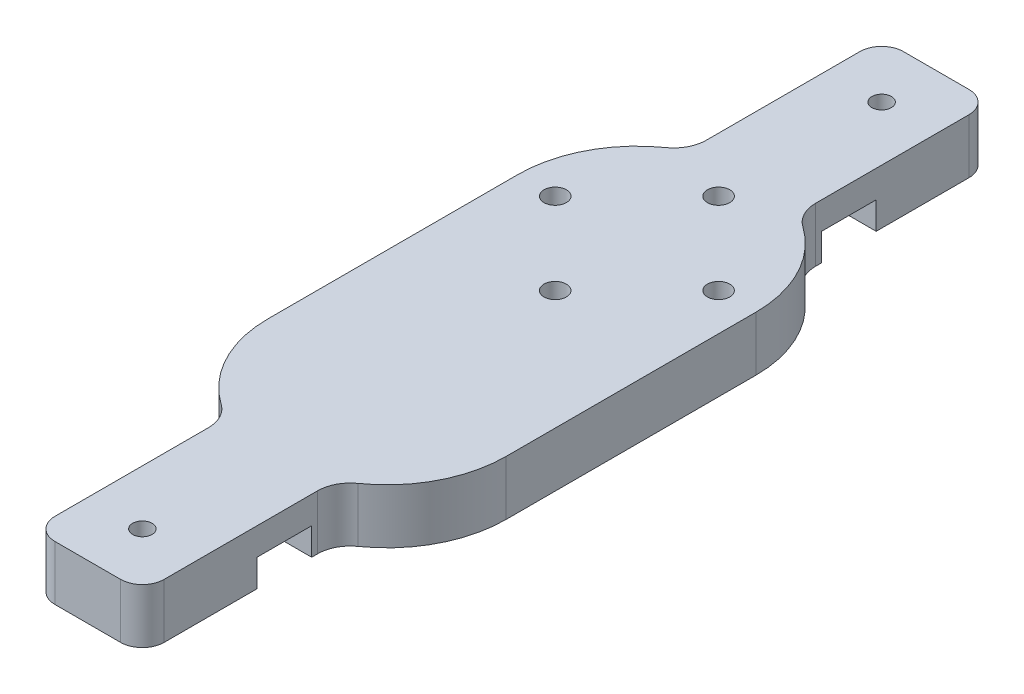
SolidWorks part; units mm, degrees
ref_plane "Front Plane" through (0, 0, 0) normal (0, 0, 1) x (1, 0, 0)
ref_plane "Top Plane" through (0, 0, 0) normal (0, 1, 0) x (1, 0, 0)
ref_plane "Right Plane" through (0, 0, 0) normal (1, 0, 0) x (0, 0, -1)
sketch "Sketch1" plane through (0, 0, 0) normal (0, 1, 0) x (1, 0, 0)
  line L0 (13.85, -23.7542) -> (13.85, 5.2917)
  line L1 (-13.85, 5.2917) -> (-13.85, -23.7542)
  line L2 (-13.85, 0) -> (13.85, 0) construction
  line L3 (0, 5.2917) -> (0, 14.7917) construction
  line L4 (0, 5.2917) -> (9.5, 5.2917) construction
  line L5 (0, 5.2917) -> (0, 14.7917) construction
  line L6 (0, 5.2917) -> (-9.5, 5.2917) construction
  line L7 (0, 5.2917) -> (0, -4.2083) construction
  line L8 (0, 0) -> (0, 40.1011) construction
  line L9 (0, 0) -> (0, -58.5637) construction
  line L10 (6.35, -36.0628) -> (6.35, -56.0237)
  line L12 (-6.35, -36.0628) -> (-6.35, -56.0237)
  line L14 (3.81, -58.5637) -> (-3.81, -58.5637)
  line L15 (3.81, 40.1011) -> (-3.81, 40.1011)
  line L16 (6.35, 17.6003) -> (6.35, 37.5611)
  line L17 (-6.35, 17.6003) -> (-6.35, 37.5611)
  line L18 (6.35, 0) -> (6.35, 40.1011) construction
  line L19 (0, 40.1011) -> (39.9619, 40.1011) construction
  line L20 (-6.35, 0) -> (-6.35, 40.1011) construction
  line L21 (-6.35, 0) -> (-6.35, -58.5637) construction
  line L22 (6.35, 0) -> (6.35, -58.5637) construction
  line L23 (39.9619, 40.1011) -> (39.9619, -58.5637) construction
  line L24 (39.9619, -58.5637) -> (0, -58.5637) construction
  line L25 (39.9619, -9.2313) -> (0, -9.2313) construction
  arc A0 (6.35, -36.0628) -> (13.85, -23.7542) centre (0, -23.7542) ccw
  arc A1 (13.85, 5.2917) -> (6.35, 17.6003) centre (0, 5.2917) ccw
  arc A2 (-13.85, -23.7542) -> (-6.35, -36.0628) centre (0, -23.7542) ccw
  circle A3 centre (0, 14.7917) radius 1.7 construction
  circle A4 centre (-9.5, 5.2917) radius 1.7 construction
  circle A5 centre (0, -4.2083) radius 1.7 construction
  circle A6 centre (9.5, 5.2917) radius 1.7 construction
  arc A7 (-6.35, 17.6003) -> (-13.85, 5.2917) centre (0, 5.2917) ccw
  arc A8 (6.35, -56.0237) -> (3.81, -58.5637) centre (3.81, -56.0237) cw
  arc A9 (-6.35, -56.0237) -> (-3.81, -58.5637) centre (-3.81, -56.0237) ccw
  arc A10 (6.35, 37.5611) -> (3.81, 40.1011) centre (3.81, 37.5611) ccw
  arc A11 (-6.35, 37.5611) -> (-3.81, 40.1011) centre (-3.81, 37.5611) cw
  circle A12 centre (0, -52.2137) radius 2.1527 construction
  circle A13 centre (0, 33.7511) radius 2.1526 construction
  point P4 (0, 5.2917)
  point P15 (0, 0)
  dimension "D2" = 13.85
  dimension "D5" = 3.4
  dimension "D3" = 2.54
  dimension "D11" = 6.35
  dimension "D12" = 4.3053
  dimension "D13" = 28.4594
  dimension "D4" = 9.5
  dimension "D6" = 40.1011
  dimension "D7" = 58.5637
  dimension "D10" = 12.7
  dimension "D14" = 6.35
  dimension "D15" = 5.2917
  dimension "D16" = 26.8315
  dimension "D17" = 26.8315
  dimension "D8" = 6.35
  dimension "D9" = 6.35
extrude "Boss-Extrude1" add sketch "Sketch1" along normal blind 6.35
sketch "Sketch3" plane through (0, 0, 0) normal (0, -1, 0) x (1, 0, 0)
  line L0 (-6.35, -23.5911) -> (6.35, -23.5911) construction
  line L1 (-6.35, -37.5611) -> (-6.35, -17.6003) construction
  line L2 (6.35, -17.6003) -> (6.35, -37.5611) construction
  line L3 (-6.35, 42.0537) -> (6.35, 42.0537) construction
  line L4 (-6.35, 36.0628) -> (-6.35, 56.0237) construction
  line L5 (6.35, 56.0237) -> (6.35, 36.0628) construction
  line L6 (0, -23.5911) -> (0, 42.0537) construction
  line L7 (-6.35, -26.7661) -> (6.35, -26.7661)
  line L8 (-6.35, 38.8787) -> (6.35, 38.8787)
  line L9 (0, 9.2313) -> (-30.9415, 9.2313) construction
  line L10 (0, -40.1011) -> (0, 58.5637) construction
  line L11 (3.81, -40.1011) -> (-3.81, -40.1011) construction
  line L12 (-3.81, 58.5637) -> (3.81, 58.5637) construction
  line L13 (-6.35, -20.4161) -> (6.35, -20.4161)
  line L14 (-6.35, 45.2287) -> (6.35, 45.2287)
  line L15 (-6.35, -26.7661) -> (-6.35, -20.4161)
  line L16 (6.35, -26.7661) -> (6.35, -20.4161)
  line L17 (-6.35, 38.8787) -> (-6.35, 45.2287)
  line L18 (6.35, 38.8787) -> (6.35, 45.2287)
  circle A0 centre (0, -23.5911) radius 1.651
  circle A1 centre (0, 42.0537) radius 1.651
  line M14 (-6.35, 56.0237) -> (-6.35, 36.0628)
  line M18 (-6.35, -17.6003) -> (-6.35, -37.5611)
  line M22 (6.35, -37.5611) -> (6.35, -17.6003)
  line M26 (6.35, 36.0628) -> (6.35, 56.0237)
  dimension "D4" = 3.302
  dimension "D1" = 16.51
  dimension "D2" = 3.175
  dimension "D3" = 3.175
extrude "Cut-Extrude2" cut sketch "Sketch3" against normal blind 3.175 contours A0 | L13 L7 A0 M18 M22 | L14 L8 A1 M14 M26 | A1
hole_wizard "#4-40 Tapped Hole1" positions "Sketch6" profile "Sketch7" tap size "#4-40" standard "ANSI Inch" end condition through all
sketch "Sketch6" plane through (0, 0, 0) normal (0, -1, 0) x (-1, 0, 0)
  point P0 (0, -52.2137)
  point P3 (0, 33.7511)
sketch "Sketch7" plane through (0, 0, 52.2137) normal (1, 0, 0) x (0, 0, -1)
  line L0 (0, 0) -> (0, 6.35)
  line L1 (0, 6.35) -> (1.1303, 6.35)
  line L2 (1.1303, 6.35) -> (1.1303, 0)
  line L5 (1.1303, 0) -> (0, 0)
  line L11 (0, -6.35) -> (0, 107.95) construction
  dimension "Thru Tap Drill Dia." = 2.2606
  dimension "Thru Tap Drill Depth" = 6.35
cosmetic thread "Hole Thread4" parameters "D2"=2.8448
cosmetic thread "Hole Thread5" parameters "D2"=2.8448
hole_wizard "M2 Clearance Hole1" positions "Sketch8" profile "Sketch9" hole size "M2" standard "ANSI Metric" end condition through all
sketch "Sketch8" plane through (0, 0, 0) normal (0, -1, 0) x (-1, 0, 0)
  point P0 (9.5, 5.2917)
  point P3 (0, 14.7917)
  point P6 (-9.5, 5.2917)
  point P9 (0, -4.2083)
sketch "Sketch9" plane through (-9.5, 0, -5.2917) normal (1, 0, 0) x (0, 0, -1)
  line L0 (0, 0) -> (0, 6.35)
  line L1 (0, 6.35) -> (1.3, 6.35)
  line L2 (1.3, 6.35) -> (1.3, 0)
  line L5 (1.3, 0) -> (0, 0)
  line L11 (0, -6.35) -> (0, 107.95) construction
  dimension "Thru Hole Dia." = 2.6
  dimension "Thru Hole Depth" = 6.35
sketch "Sketch10" plane through (0, 0, 0) normal (0, -1, 0) x (1, 0, 0)
  line L0 (9.5, -5.2917) -> (-9.5, -5.2917) construction
  circle A0 centre (0, -5.2917) radius 12.7
  circle A1 centre (-9.5, -5.2917) radius 2.75
  dimension "D1" = 5.5
  dimension "D2" = 25.4
  dimension "D3" = 0.45
fillet "Fillet1" radius 3.81 4 edges at (-6.35, 3.175, 36.0628) (-6.35, 3.175, -17.6003) (6.35, 3.175, 36.0628) (6.35, 3.175, -17.6003)
